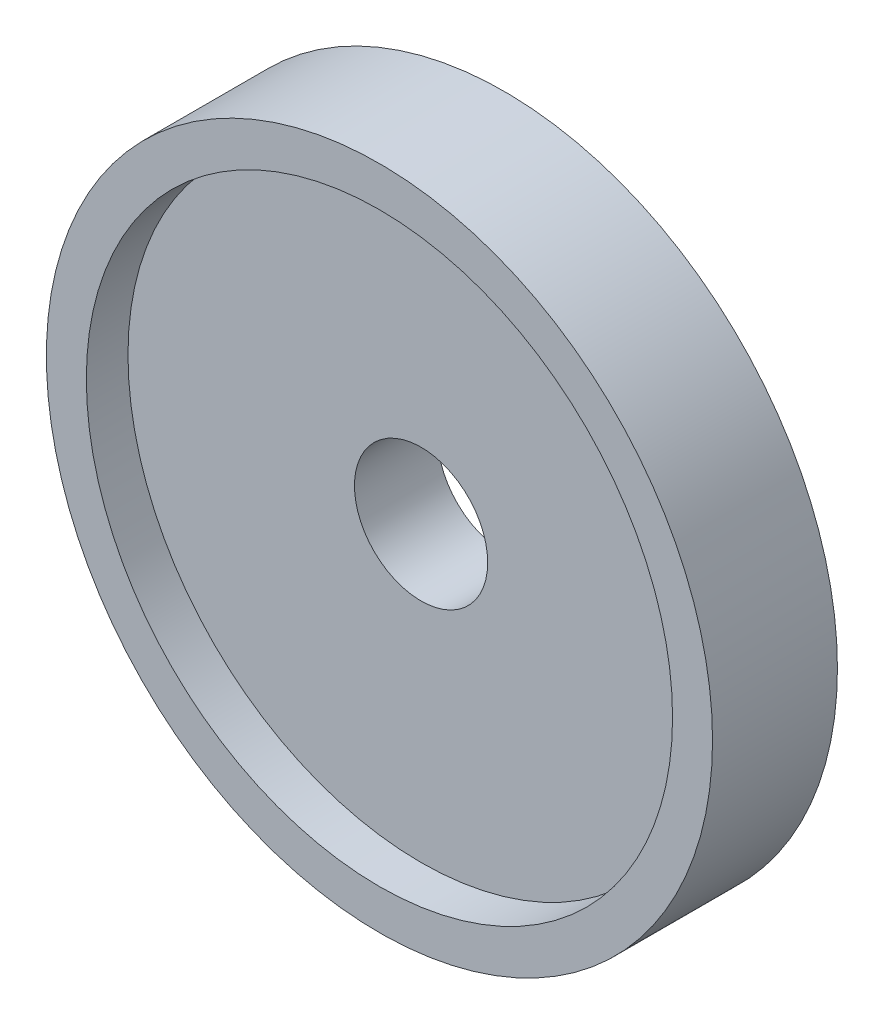
SolidWorks part; units mm, degrees
ref_plane "Front Plane" through (0, 0, 0) normal (0, 0, 1) x (1, 0, 0)
ref_plane "Top Plane" through (0, 0, 0) normal (0, 1, 0) x (1, 0, 0)
ref_plane "Right Plane" through (0, 0, 0) normal (1, 0, 0) x (0, 0, -1)
sketch "Sketch1" plane through (0, 0, 0) normal (0, 0, 1) x (1, 0, 0)
  circle A0 centre (0, 0) radius 2
  dimension "D1" = 4
extrude "Boss-Extrude2" add sketch "Sketch1" along normal blind 0.75
sketch "Sketch3" plane through (0, 0, 0.75) normal (0, 0, 1) x (1, 0, 0)
  circle A0 centre (0, 0) radius 1.76
  dimension "D1" = 3.52
extrude "Cut-Extrude1" cut sketch "Sketch3" against normal blind 0.25
sketch "Sketch4" plane through (0, 0, 0.5) normal (0, 0, 1) x (1, 0, 0)
  circle A0 centre (0, 0) radius 0.4
  dimension "D1" = 0.8
extrude "Cut-Extrude2" cut sketch "Sketch4" against normal through all
